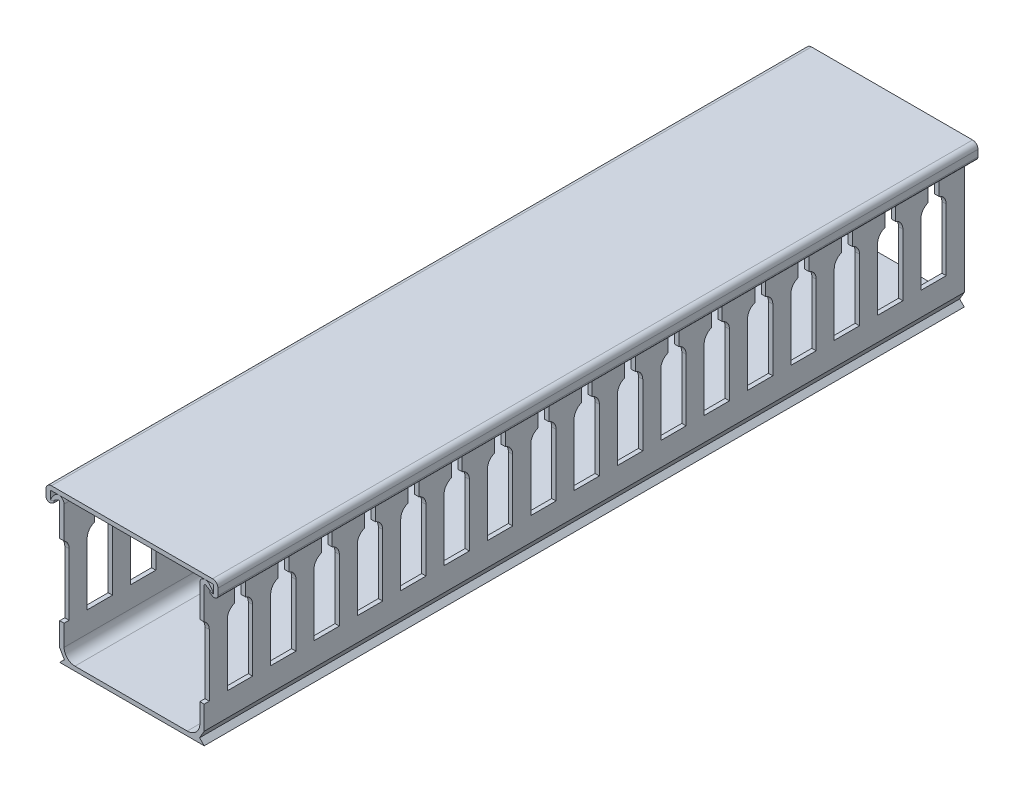
SolidWorks part; units mm, degrees
ref_plane "Front Plane" through (0, 0, 0) normal (0, 0, 1) x (1, 0, 0)
ref_plane "Top Plane" through (0, 0, 0) normal (0, 1, 0) x (1, 0, 0)
ref_plane "Right Plane" through (0, 0, 0) normal (1, 0, 0) x (0, 0, -1)
sketch "Sketch1" plane through (0, 0, 0) normal (0, 0, 1) x (1, 0, 0)
  line L0 (-20, 0) -> (20, 0)
  line L1 (-20, 3.5) -> (-20, 38.546)
  line L2 (-20, 0) -> (-18.7189, 1.2811)
  line L3 (-18.7189, 1.2811) -> (-20, 3.5)
  line L4 (-22.4196, 37.589) -> (-20.381, 38.766)
  line L5 (0, 0) -> (0, -17.0643) construction
  line L6 (22.4196, 37.589) -> (22.5, 37.889)
  line L7 (22.4196, 37.589) -> (20.381, 38.766)
  line L8 (20, 3.5) -> (20, 38.546)
  line L9 (18.7189, 1.2811) -> (20, 3.5)
  line L10 (-22.4196, 37.589) -> (-22.5, 37.889)
  line L11 (20, 0) -> (18.7189, 1.2811)
  line L12 (-18.8, 4.2) -> (-18.8, 38.546)
  line L13 (18.8, 3.5) -> (18.8, 38.546) construction
  line L14 (-17.2865, 1.2) -> (20, 1.2) construction
  line L15 (-15.8, 1.2) -> (15.3, 1.2)
  line L16 (18.8, 4.7) -> (18.8, 38.546)
  line L17 (-17.2865, 1.2) -> (-18.8, 3.8215) construction
  line L18 (-17.2865, 1.2) -> (-17.2865, 1.2) construction
  line L19 (-18.8, 3.8215) -> (-18.8, 38.546) construction
  arc A0 (-22.5, 37.889) -> (-21.2623, 39.5936) centre (-17.1014, 35.2708) cw
  arc A1 (22.5, 37.889) -> (21.2623, 39.5936) centre (17.1014, 35.2708) ccw
  arc A2 (20.381, 38.766) -> (20, 38.546) centre (20.254, 38.546) ccw
  arc A3 (-21.2623, 39.5936) -> (-18.8, 38.546) centre (-20.254, 38.546) cw
  arc A4 (21.2623, 39.5936) -> (18.8, 38.546) centre (20.254, 38.546) ccw
  arc A5 (-15.8, 1.2) -> (-18.8, 4.2) centre (-15.8, 4.2) cw
  arc A6 (-20.381, 38.766) -> (-20, 38.546) centre (-20.254, 38.546) cw
  arc A7 (15.3, 1.2) -> (18.8, 4.7) centre (15.3, 4.7) ccw
  arc A8 (-20.981, 39.8052) -> (-18.8, 38.546) centre (-20.254, 38.546) cw construction
  arc A9 (20.981, 39.8052) -> (18.8, 38.546) centre (20.254, 38.546) ccw construction
  dimension "D1" = 0.3
  dimension "D2" = 6
  dimension "D3" = 60
  dimension "D5" = 0.254
  dimension "D6" = 1.2
  dimension "D11" = 3
  dimension "D13" = 3.5
  dimension "D14" = 40
  dimension "D7" = 45
  dimension "D8" = 30
  dimension "D4" = 75
  dimension "D9" = 3.5
  dimension "D10" = 2.5
  dimension "D12" = 40
extrude "Boss-Extrude2" add sketch "Sketch1" along normal mid plane 1000 contours L0 L11 L9 L8 A2 L7 L6 A1 A4 L16 A7 L15 A5 L12 A3 A0 L10 L4 A6 L1 L3 L2
sketch "Sketch2" plane through (0, 0, 0) normal (1, 0, 0) x (0, 0, -1)
  line L0 (490, 30) -> (490, 40)
  line L1 (-500, 0) -> (500, 0) construction
  line L2 (500, 3.5) -> (500, 38.546) construction
  line L3 (488, 10) -> (495, 10)
  line L4 (495, 10) -> (495, 27.1716)
  line L6 (490, 40) -> (493, 40)
  line L7 (493, 30) -> (493, 40)
  line L8 (488, 10) -> (488, 27.1716)
  line L10 (500, 40) -> (-500, 40) construction
  arc A0 (495, 27.1716) -> (493, 30) centre (492, 27.1716) ccw
  arc A1 (488, 27.1716) -> (490, 30) centre (491, 27.1716) cw
  point P22 (491.5, 10)
  point P23 (491.5, 40)
  dimension "D1" = 3
  dimension "D2" = 10
  dimension "D3" = 10
  dimension "D4" = 7
  dimension "D5" = 5
  dimension "D6" = 3
extrude "Cut-Extrude1" cut sketch "Sketch2" against normal blind 82.296 and the other way blind 151.13
pattern_linear "LPattern1" count 83 spacing 12 along (0, 0, 1) of "Cut-Extrude1"
sketch "Sketch3" plane through (0, 0, -500) normal (0, 0, 1) x (1, 0, 0)
  line L0 (-22.6, 37.9) -> (-22.6, 39.7) construction
  line L1 (-22.6, 37.8781) -> (-22.6, 39.7)
  line L2 (22.3, 40) -> (-22.3, 40)
  line L4 (22.6, 37.8781) -> (22.6, 39.7)
  line L5 (22.6, 37.9) -> (22.6, 39.7) construction
  line L6 (22.3, 41.2) -> (-22.3, 41.2)
  line L7 (-22.3, 37.034) -> (-21.6, 37.4381)
  line L8 (-21.6, 37.4381) -> (-21.6, 38.0155)
  line L9 (-23.8, 37.9) -> (-23.8, 39.7)
  line L10 (-21.6, 38.0155) -> (-22.219, 37.6581)
  line L12 (22.3, 37.034) -> (21.6, 37.4381)
  line L14 (21.6, 38.0155) -> (22.219, 37.6581)
  line L15 (23.8, 37.9) -> (23.8, 39.7)
  line L16 (21.6, 37.4381) -> (21.6, 38.0155)
  arc A0 (-23.8, 37.9) -> (-22.3, 37.034) centre (-22.8, 37.9) ccw
  arc A1 (-22.6, 37.8781) -> (-22.219, 37.6581) centre (-22.346, 37.8781) ccw
  arc A2 (22.3, 37.034) -> (23.8, 37.9) centre (22.8, 37.9) ccw
  arc A3 (-22.3, 41.2) -> (-23.8, 39.7) centre (-22.3, 39.7) ccw
  arc A4 (-22.3, 40) -> (-22.6, 39.7) centre (-22.3, 39.7) ccw
  arc A5 (22.3, 41.2) -> (23.8, 39.7) centre (22.3, 39.7) cw
  arc A6 (22.3, 40) -> (22.6, 39.7) centre (22.3, 39.7) cw
  arc A7 (22.6, 37.8781) -> (22.219, 37.6581) centre (22.346, 37.8781) cw
  arc A9 (-18.8, 38.546) -> (-21.2623, 39.5936) centre (-20.254, 38.546) ccw construction
  point P35 (0, 40)
  dimension "D2" = 2.2
  dimension "D3" = 0.254
  dimension "D4" = 2.2
  dimension "D5" = 1.5
  dimension "D7" = 4.3
  dimension "D12" = 1
  dimension "D6" = 60
  dimension "D8" = 60
  dimension "D9" = 0.5
  dimension "D11" = 0.1
  dimension "D10" = 1.2
extrude "Boss-Extrude3" add sketch "Sketch3" along normal up to vertex separate body
sketch "Sketch4" plane through (0, 0, 500) normal (0, 0, 1) x (1, 0, 0)
  line L1 (-28.3457, 44.3252) -> (25.8852, 44.3252)
  line L2 (-28.3457, 44.3252) -> (-28.3457, -2.0319)
  line L3 (-28.3457, -2.0319) -> (25.8852, -2.0319)
  line L4 (25.8852, 44.3252) -> (25.8852, -2.0319)
extrude "Cut-Extrude2" cut sketch "Sketch4" against normal blind 742
sketch "Sketch5" plane through (0, 0, -242) normal (0, 0, 1) x (1, 0, 0)
  line L1 (-26.0067, 44.1693) -> (24.6779, 44.1693)
  line L2 (-26.0067, 44.1693) -> (-26.0067, -1.39)
  line L3 (-26.0067, -1.39) -> (24.6779, -1.39)
  line L4 (24.6779, 44.1693) -> (24.6779, -1.39)
extrude "Cut-Extrude3" cut sketch "Sketch5" against normal blind 47.6
